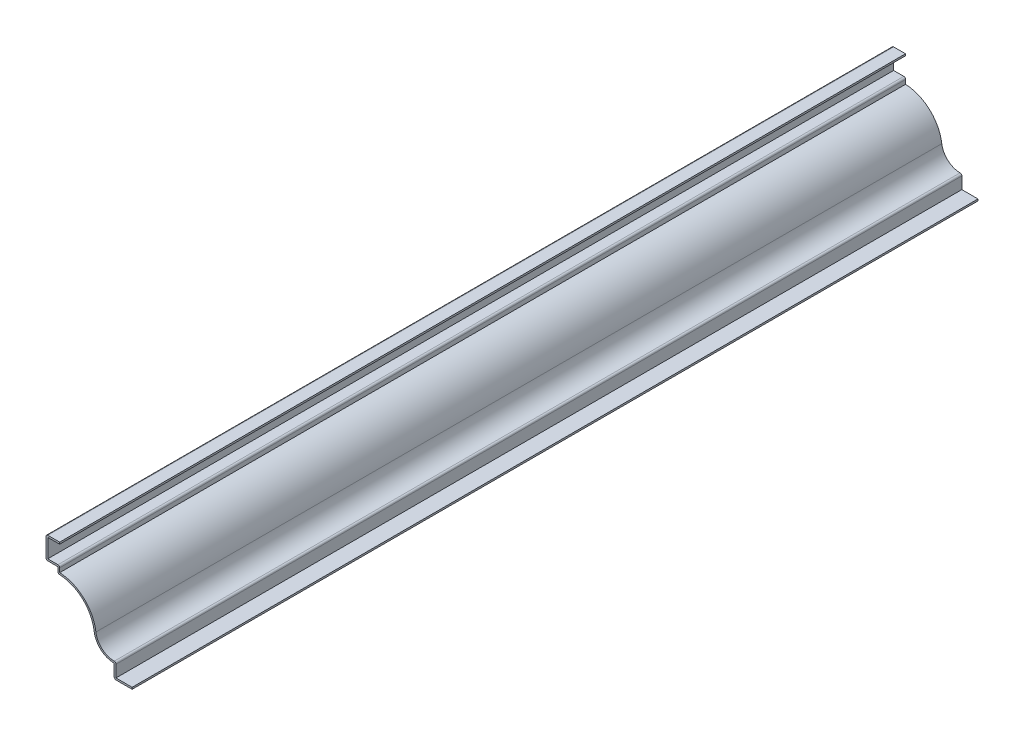
SolidWorks part; units mm, degrees
ref_plane "Front Plane" through (0, 0, 0) normal (0, 0, 1) x (1, 0, 0)
ref_plane "Top Plane" through (0, 0, 0) normal (0, 1, 0) x (1, 0, 0)
ref_plane "Right Plane" through (0, 0, 0) normal (1, 0, 0) x (0, 0, -1)
sketch "Sketch1" plane through (0, 0, 0) normal (0, 0, 1) x (1, 0, 0)
  line L0 (0, 0) -> (-16.6687, 0)
  line L1 (-16.6687, 0) -> (-16.6687, 12.7)
  line L2 (-69.0562, 58.7375) -> (-69.0562, 64.2938)
  line L3 (-69.0562, 64.2938) -> (-80.1687, 64.2938)
  line L4 (-80.1687, 64.2938) -> (-80.1687, 84.9313)
  line L5 (-80.1687, 84.9313) -> (-67.4687, 84.9313)
  arc A0 (-16.6687, 12.7) -> (-35.3478, 29.1149) centre (-16.6687, 31.5352) cw
  arc A1 (-35.3478, 29.1149) -> (-69.0562, 58.7375) centre (-69.0563, 24.7473) ccw
  point P8 (-69.0563, 61.5156)
  point P13 (-37.6366, 32.5412)
  point P14 (-35.2922, 32.6975)
  point P15 (0, 0)
  point P16 (0, 0)
  point P17 (0, 0)
  point P18 (-35.3478, 29.1149)
  dimension "D1" = 84.9313
  dimension "D2" = 12.7
  dimension "D3" = 16.6687
  dimension "D4" = 52.3875
  dimension "D5" = 11.1125
  dimension "D6" = 67.4687
  dimension "D7" = 12.7
  dimension "D8" = 46.0375
  dimension "D9" = 5.5562
extrude "Extrude-Thin1" add sketch "Sketch1" against normal blind 787.4 thin
fillet "Fillet1" radius 1.651 6 edges at (-16.6687, 0, -393.7) (-15.0177, 14.4305, -393.7) (-69.0562, 58.7375, -393.7) (-67.4052, 65.9447, -393.7) (-80.1687, 64.2938, -393.7) (-80.1687, 84.9313, -393.7)
